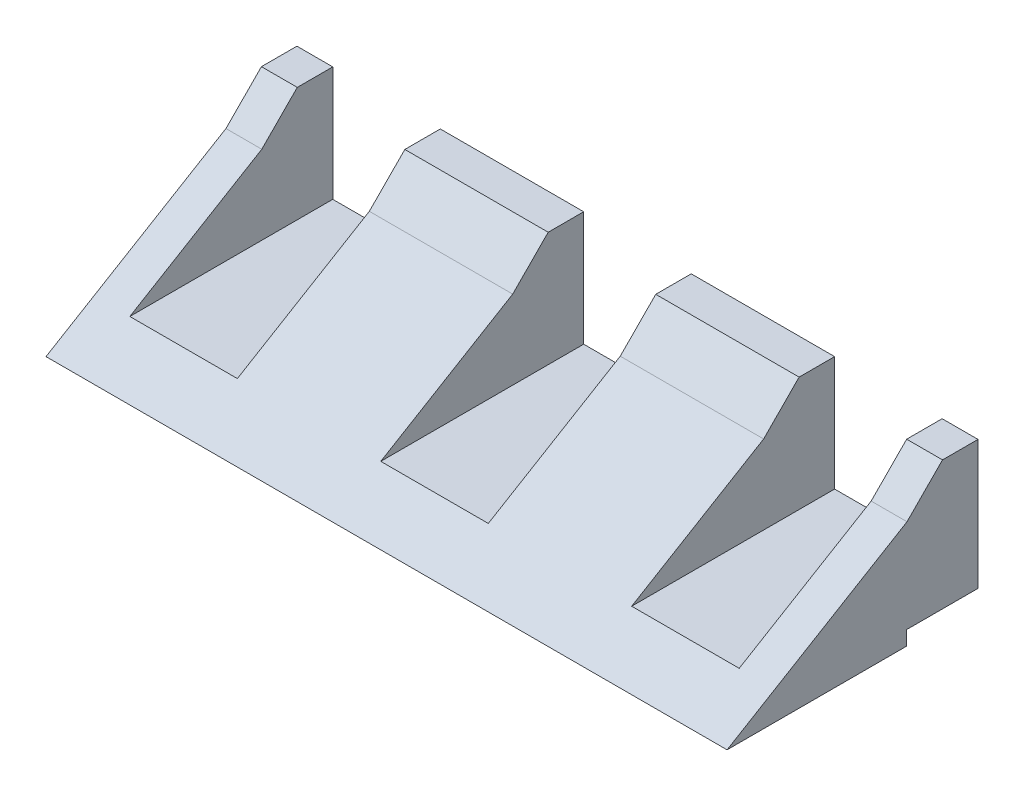
SolidWorks part; units mm, degrees
ref_plane "Alzado" through (0, 0, 0) normal (0, 0, 1) x (1, 0, 0)
ref_plane "Planta" through (0, 0, 0) normal (0, 1, 0) x (1, 0, 0)
ref_plane "Vista lateral" through (0, 0, 0) normal (1, 0, 0) x (0, 0, -1)
sketch "Croquis1" plane through (0, 0, 0) normal (0, 1, 0) x (1, 0, 0)
  line L1 (40.2047, -24.1228) -> (-59.7953, -24.1228)
  line L2 (40.2047, -24.1228) -> (40.2047, 60.8772)
  line L3 (40.2047, 60.8772) -> (-59.7953, 60.8772)
  line L4 (-59.7953, -24.1228) -> (-59.7953, 60.8772)
  dimension "D1" = 100
  dimension "D2" = 85
extrude "Saliente-Extruir1" add sketch "Croquis1" along normal blind 20
sketch "Croquis2" plane through (0, 20, 0) normal (0, 1, 0) x (1, 0, 0)
  line L0 (-59.7953, -24.1228) -> (-59.7953, 10.8772)
  line L1 (-59.7953, 60.8772) -> (-59.7953, -24.1228) construction
  line L2 (-59.7953, 10.8772) -> (40.2047, 10.8772)
  line L3 (40.2047, -24.1228) -> (40.2047, 60.8772) construction
  line L4 (40.2047, 10.8772) -> (40.2047, -24.1228)
  line L5 (40.2047, -24.1228) -> (-59.7953, -24.1228)
  dimension "D1" = 35
sketch "Croquis3" plane through (40.2047, 0, 0) normal (1, 0, 0) x (0, 0, -1)
  line L0 (10.9765, 20) -> (0.9765, 20)
  line L1 (10.8772, 20) -> (-24.1228, 20) construction
  line L2 (-24.1228, 20) -> (10.8772, 20) construction
  line L3 (0.9765, 20) -> (-24.1228, 0)
  line L4 (10.9765, 20) -> (10.9765, 0)
  line L5 (-24.1228, 0) -> (60.8772, 0) construction
  line L6 (10.9765, 0) -> (-24.1228, 0)
  line L7 (-24.1228, 0) -> (-24.1228, 20)
  line L8 (-24.1228, 20) -> (0.9765, 20)
  line M4 (60.8772, 20) -> (-24.1228, 20)
  line M5 (-24.1228, 20) -> (-24.1228, 0)
  dimension "D1" = 10
extrude "Cortar-Extruir1" cut sketch "Croquis3" against normal up to next contours L3 M4 M5
sketch "Croquis4" plane through (40.2047, 0, 0) normal (1, 0, 0) x (0, 0, -1)
  line L0 (0.9765, 20) -> (0.9765, 15)
  line L1 (0.9765, 15) -> (-24.1228, 0)
  line L2 (-24.1228, 0) -> (0.9765, 20)
  dimension "D1" = 5
extrude "Cortar-Extruir2" cut sketch "Croquis4" against normal up to next
ref_plane "Plano1" through (0, 0, -11) normal (0, 0, 1) x (1, 0, 0)
sketch "Croquis7" plane through (0, 0, -11) normal (0, 0, 1) x (1, 0, 0)
  line L0 (40.2047, 20) -> (35.2047, 20)
  line L1 (-59.7953, 20) -> (40.2047, 20) construction
  line L2 (35.2047, 20) -> (35.2047, 4)
  line L3 (35.2047, 4) -> (20.2047, 4)
  line L4 (20.2047, 4) -> (20.2047, 20)
  line L5 (20.2047, 20) -> (0.2047, 20)
  line L6 (0.2047, 20) -> (0.2047, 4)
  line L7 (0.2047, 4) -> (-14.7953, 4)
  line L8 (-14.7953, 4) -> (-14.7953, 20)
  line L9 (-14.7953, 20) -> (-34.7953, 20)
  line L10 (-34.7953, 20) -> (-34.7953, 4)
  line L11 (-34.7953, 4) -> (-49.7953, 4)
  line L12 (-49.7953, 4) -> (-49.7953, 20)
  line L13 (-49.7953, 20) -> (-54.7953, 20)
  line L14 (-54.7953, 20) -> (-54.7953, 0)
  line L15 (-59.7953, 0) -> (40.2047, 0) construction
  line L16 (-54.7953, 0) -> (-59.7953, 0)
  line L17 (-59.7953, 0) -> (-59.7953, 20)
  line L18 (-59.7953, 20) -> (-54.7953, 20)
  dimension "D1" = 5
  dimension "D2" = 16
  dimension "D3" = 15
  dimension "D4" = 20
  dimension "D5" = 16
  dimension "D6" = 15
  dimension "D7" = 20
  dimension "D8" = 16
  dimension "D9" = 15
  dimension "D10" = 5
sketch "Croquis8" plane through (-59.7953, 0, 0) normal (-1, 0, 0) x (0, 0, 1)
  line L0 (-11, 20) -> (-0.9765, 20)
  line L1 (-11, 4) -> (-11, 20) construction
  line L2 (-11, 20) -> (-11, 4) construction
  line L3 (-0.9765, 20) -> (-0.9765, 15)
  line L4 (-0.9765, 15) -> (24.1228, 0)
  line L5 (24.1228, 0) -> (-11, 0)
  line L6 (-11, 0) -> (-11, 20) construction
  line L7 (-11, 20) -> (-11, 0) construction
  line L8 (-11, 0) -> (-11, 20)
extrude "Cortar-Extruir6" cut sketch "Croquis8" against normal blind 5
sketch "Croquis11" plane through (0, 0, -11) normal (0, 0, 1) x (1, 0, 0)
  line L0 (35.2047, 20) -> (20.2047, 20)
  line L1 (20.2047, 20) -> (20.2047, 4)
  line L2 (20.2047, 4) -> (35.2047, 4)
  line L3 (35.2047, 4) -> (35.2047, 20)
  line L4 (0.2047, 20) -> (-14.7953, 20)
  line L5 (-14.7953, 20) -> (-14.7953, 4)
  line L6 (-14.7953, 4) -> (0.2047, 4)
  line L7 (0.2047, 4) -> (0.2047, 18.8818)
  line L8 (0.2047, 20) -> (0.2047, 4) construction
  line L9 (0.2047, 18.8818) -> (0.2047, 20)
  line L10 (-34.7953, 20) -> (-49.7953, 20)
  line L11 (-49.7953, 20) -> (-49.7953, 4)
  line L12 (-49.7953, 4) -> (-34.7953, 4)
  line L13 (-34.7953, 4) -> (-34.7953, 20)
extrude "Cortar-Extruir7" cut sketch "Croquis11" along normal blind 44
sketch "Croquis12" plane through (0, 20, 0) normal (0, 1, 0) x (1, 0, 0)
  line L0 (-59.7953, 11) -> (-54.7953, 11)
  line L1 (-54.7953, 11) -> (-54.7953, 60.8772)
  line L2 (40.2047, 60.8772) -> (-59.7953, 60.8772) construction
  line L3 (-54.7953, 60.8772) -> (-59.7953, 60.8772)
  line L4 (-59.7953, 60.8772) -> (-59.7953, 11)
extrude "Cortar-Extruir8" cut sketch "Croquis12" against normal blind 44
sketch "Croquis13" plane through (40.2047, 0, 0) normal (1, 0, 0) x (0, 0, -1)
  line L0 (60.8772, 0) -> (60.8772, 2)
  line L1 (60.8772, 20) -> (60.8772, 0) construction
  line L2 (60.8772, 2) -> (60.8772, 20)
  line L3 (60.8772, 20) -> (10.8772, 20)
  line L4 (0.9765, 20) -> (60.8772, 20) construction
  line L5 (10.8772, 20) -> (10.8772, 2)
  line L6 (10.8772, 2) -> (60.8772, 2)
  line M3 (60.8772, 20) -> (0.9765, 20)
  line M7 (60.8772, 0) -> (60.8772, 20)
  dimension "D1" = 2
  dimension "D2" = 50
extrude "Cortar-Extruir9" cut sketch "Croquis13" against normal up to next contours L5 L6 M7 M3
sketch "Croquis14" plane through (40.2047, 0, 0) normal (1, 0, 0) x (0, 0, -1)
  line L0 (-24.1228, 0) -> (0.8772, 0)
  line L1 (-24.1228, 0) -> (60.8772, 0) construction
  line L2 (0.8772, 0) -> (0.8772, 2)
  line L3 (0.8772, 0) -> (10.6821, 0)
  line L4 (10.6821, 0) -> (10.6821, 2)
  line L5 (10.6821, 2) -> (0.8772, 2)
  line M7 (-24.1228, 0) -> (60.8772, 0)
  dimension "D1" = 25
  dimension "D2" = 2
extrude "Cortar-Extruir10" cut sketch "Croquis14" against normal blind 121 contours L4 L5 L2 M7
sketch "Croquis17" plane through (40.2047, 0, 0) normal (1, 0, 0) x (0, 0, -1)
  line L0 (10.8772, 2) -> (10.6821, 0)
  line L1 (10.6821, 0) -> (60.8772, 0)
  line L2 (60.8772, 0) -> (60.8772, 2)
  line L3 (60.8772, 2) -> (10.8772, 2)
extrude "Cortar-Extruir11" cut sketch "Croquis17" against normal up to next
sketch "Croquis18" plane through (40.2047, 0, 0) normal (1, 0, 0) x (0, 0, -1)
  line L0 (10.6821, 2) -> (10.8772, 2)
  line L1 (10.8772, 2) -> (10.6821, 0)
  line L2 (10.6821, 0) -> (10.6821, 2)
extrude "Cortar-Extruir12" cut sketch "Croquis18" against normal up to next
sketch "Croquis19" plane through (-54.7953, 0, 0) normal (-1, 0, 0) x (0, 0, 1)
  line L0 (-0.9765, 15) -> (-5.9268, 20)
  line L1 (-0.9765, 20) -> (-10.8772, 20) construction
  line L2 (-5.9268, 20) -> (-0.9765, 20)
  line L3 (-0.9765, 20) -> (-0.9765, 15)
extrude "Cortar-Extruir13" cut sketch "Croquis19" against normal blind 96
sketch "Croquis21" plane through (-54.7953, 0, 0) normal (-1, 0, 0) x (0, 0, 1)
  line L0 (-0.9765, 15) -> (24.1228, 0)
